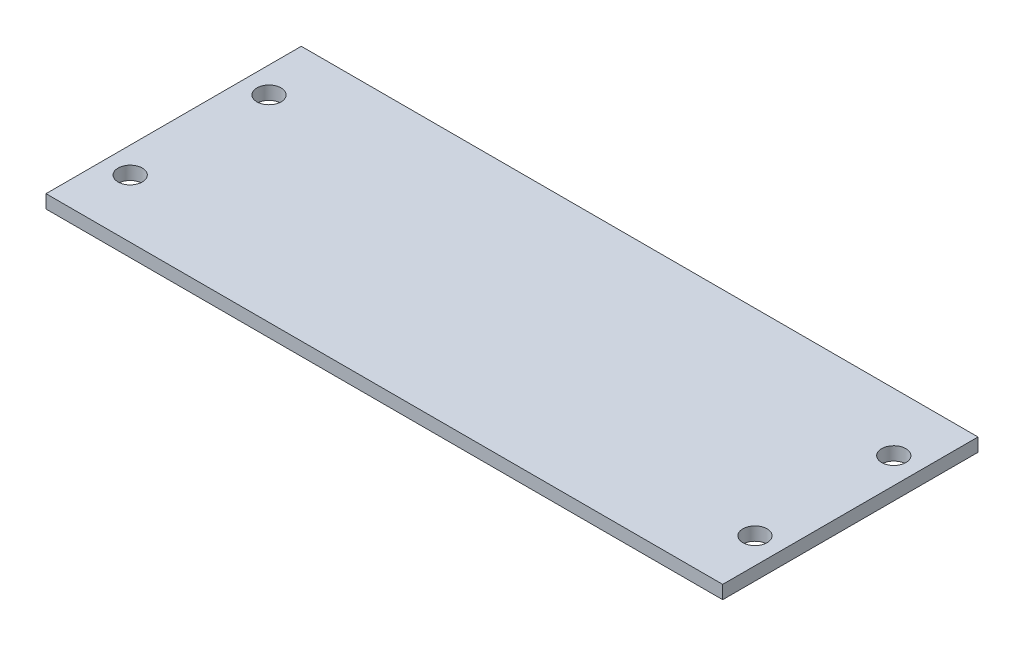
SolidWorks part; units mm, degrees
ref_plane "Front Plane" through (0, 0, 0) normal (0, 0, 1) x (1, 0, 0)
ref_plane "Top Plane" through (0, 0, 0) normal (0, 1, 0) x (1, 0, 0)
ref_plane "Right Plane" through (0, 0, 0) normal (1, 0, 0) x (0, 0, -1)
sketch "Sketch1" plane through (0, 0, 0) normal (0, 1, 0) x (1, 0, 0)
  line L1 (0, 0) -> (55.88, 0)
  line L2 (0, 0) -> (0, 21.082)
  line L3 (0, 21.082) -> (55.88, 21.082)
  line L4 (55.88, 0) -> (55.88, 21.082)
  circle A0 centre (2.143, 16.272) radius 1
  circle A1 centre (2.143, 4.81) radius 1
  circle A2 centre (53.737, 16.272) radius 1
  circle A3 centre (53.737, 4.81) radius 1
  point P13 (2.143, 17.272)
  point P14 (1.143, 16.272)
  point P15 (1.143, 4.81)
  point P16 (2.143, 3.81)
  point P17 (53.737, 3.81)
  point P18 (54.737, 4.81)
  point P19 (53.737, 17.272)
  point P20 (54.737, 16.272)
  point P21 (5.5297, 4.8753)
  point P22 (0, 0)
  point P23 (0, 0)
  point P24 (0, 0)
  point P25 (0, 0)
  point P26 (0, 0)
  dimension "D1" = 21.082
  dimension "D3" = 2
  dimension "D2" = 55.88
  dimension "D4" = 3.81
  dimension "D5" = 3.81
  dimension "D6" = 1.143
  dimension "D7" = 1.143
extrude "Boss-Extrude1" add sketch "Sketch1" along normal blind 1.1
